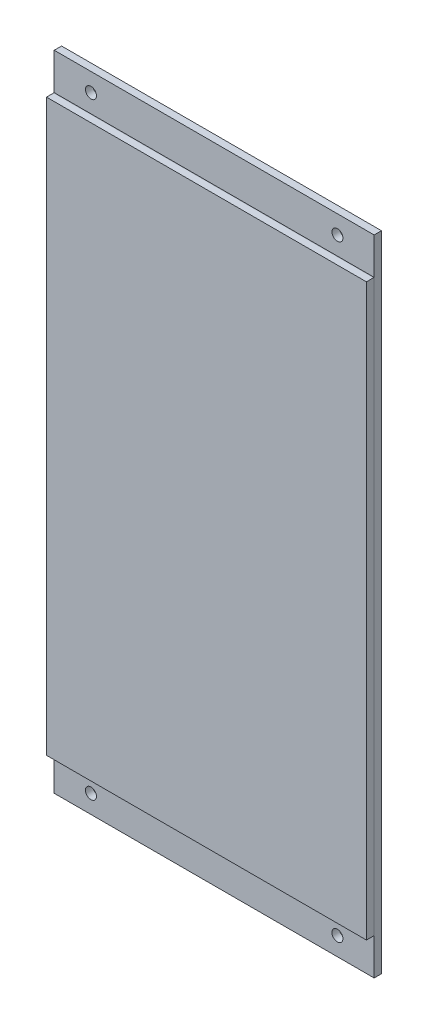
SolidWorks part; units mm, degrees
ref_plane "Alzado" through (0, 0, 0) normal (0, 0, 1) x (1, 0, 0)
ref_plane "Planta" through (0, 0, 0) normal (0, 1, 0) x (1, 0, 0)
ref_plane "Vista lateral" through (0, 0, 0) normal (1, 0, 0) x (0, 0, -1)
sketch "Sketch1" plane through (0, 0, 0) normal (0, 0, 1) x (1, 0, 0)
  line L1 (-16.5216, 27.4671) -> (70.5784, 27.4671)
  line L2 (-16.5216, 27.4671) -> (-16.5216, -127.7329)
  line L3 (-16.5216, -127.7329) -> (70.5784, -127.7329)
  line L4 (70.5784, 27.4671) -> (70.5784, -127.7329)
  dimension "D1" = 87.1
  dimension "D2" = 155.2
extrude "Boss-Extrude1" add sketch "Sketch1" along normal blind 2
sketch "Sketch3" plane through (0, 0, 0) normal (0, 0, -1) x (-1, 0, 0)
  line L1 (-70.5784, 27.4671) -> (16.5216, 27.4671)
  line L2 (-70.5784, 27.4671) -> (-70.5784, -127.7329)
  line L3 (-70.5784, -127.7329) -> (16.5216, -127.7329)
  line L4 (16.5216, 27.4671) -> (16.5216, -127.7329)
extrude "Boss-Extrude3" add sketch "Sketch3" along normal blind 0.1 separate body
sketch "Sketch4" plane through (0, 0, -0.1) normal (0, 0, -1) x (-1, 0, 0)
  line L0 (-70.5784, -127.7329) -> (16.5216, -127.7329) construction
  line L1 (-70.5784, 37.4671) -> (16.5216, 37.4671)
  line L2 (-70.5784, 37.4671) -> (-70.5784, -137.7329)
  line L3 (-70.5784, -137.7329) -> (16.5216, -137.7329)
  line L4 (16.5216, 37.4671) -> (16.5216, -137.7329)
  line L5 (-70.5784, 37.4671) -> (16.5216, -137.7329) construction
  line L6 (-70.5784, -137.7329) -> (16.5216, 37.4671) construction
  line L7 (16.5216, 27.4671) -> (-70.5784, 27.4671) construction
  point P0 (-27.0284, -50.1329)
  dimension "D1" = 10
  dimension "D2" = 10
extrude "Boss-Extrude4" add sketch "Sketch4" along normal blind 2 separate body
sketch "Sketch5" plane through (0, 0, -0.1) normal (0, 0, 1) x (1, 0, 0)
  line L0 (-16.5216, 37.4671) -> (70.5784, 37.4671) construction
  line L1 (70.5784, 37.4671) -> (70.5784, -137.7329) construction
  line L2 (-16.5216, -137.7329) -> (-16.5216, 37.4671) construction
  line L3 (70.5784, -137.7329) -> (-16.5216, -137.7329) construction
  circle A0 centre (-6.5216, 32.4671) radius 1.5
  circle A1 centre (60.5784, 32.4671) radius 1.5
  circle A2 centre (-6.5216, -132.7329) radius 1.5
  circle A3 centre (60.5784, -132.7329) radius 1.5
  dimension "D1" = 5
  dimension "D2" = 5
  dimension "D5" = 5
  dimension "D3" = 10
  dimension "D4" = 10
  dimension "D6" = 5
extrude "Cut-Extrude1" cut sketch "Sketch5" against normal blind 2
